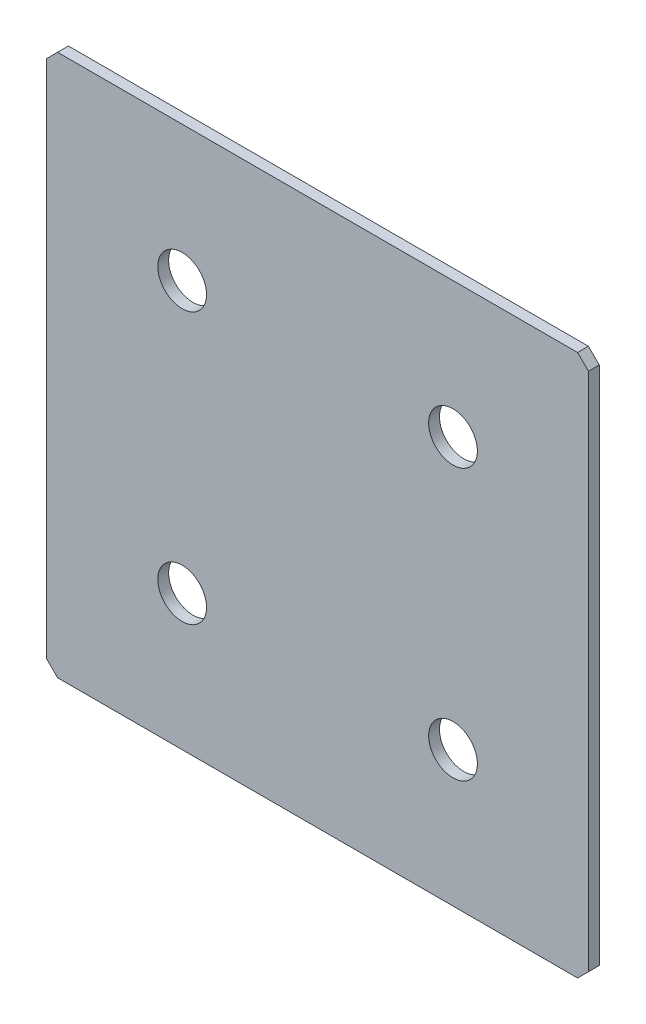
SolidWorks part; units mm, degrees
material "Простая углеродистая сталь"
ref_plane "Спереди(Плоскость XY)" through (0, 0, 0) normal (0, 0, 1) x (1, 0, 0)
ref_plane "Сверху(Плоскость XZ)" through (0, 0, 0) normal (0, 1, 0) x (1, 0, 0)
ref_plane "Справа(Плоскость ZY)" through (0, 0, 0) normal (1, 0, 0) x (0, 0, -1)
sketch "Эскиз1" plane through (0, 0, 0) normal (0, 0, 1) x (1, 0, 0)
  line L1 (-50, -50) -> (50, -50)
  line L2 (-50, -50) -> (-50, 50)
  line L3 (-50, 50) -> (50, 50)
  line L4 (50, -50) -> (50, 50)
  line L5 (-50, -50) -> (50, 50) construction
  line L6 (-50, 50) -> (50, -50) construction
  point P0 (0, 0)
  dimension "D1" = 100
  dimension "D2" = 100
extrude "Бобышка-Вытянуть1" add sketch "Эскиз1" along normal blind 2
chamfer "Фаска1" distance 2 angle 45 4 edges at (-50, -50, 1) (50, -50, 1) (-50, 50, 1) (50, 50, 1)
hole_wizard "Отверстие с зазором M81" positions "Эскиз2" profile "Эскиз3" hole size "M8" standard "DIN" end condition through all
sketch "Эскиз2" plane through (0, 0, 2) normal (0, 0, 1) x (1, 0, 0)
  line L2 (-25, 25) -> (25, 25) construction
  line L7 (-25, -25) -> (25, -25) construction
  line L11 (0, 25) -> (0, -25) construction
  point P0 (-25, 25)
  point P2 (25, 25)
  point P8 (-25, -25)
  point P10 (25, -25)
  dimension "D1" = 50
sketch "Эскиз3" plane through (-25, 25, 2) normal (1, 0, 0) x (0, -1, 0)
  line L0 (0, 0) -> (0, 2)
  line L1 (0, 2) -> (4.5, 2)
  line L2 (4.5, 2) -> (4.5, 0)
  line L5 (4.5, 0) -> (0, 0)
  line L11 (0, -6.35) -> (0, 107.95) construction
  dimension "Диаметр сквозного отверстия" = 9
  dimension "Глубина сквозного отверстия" = 2
